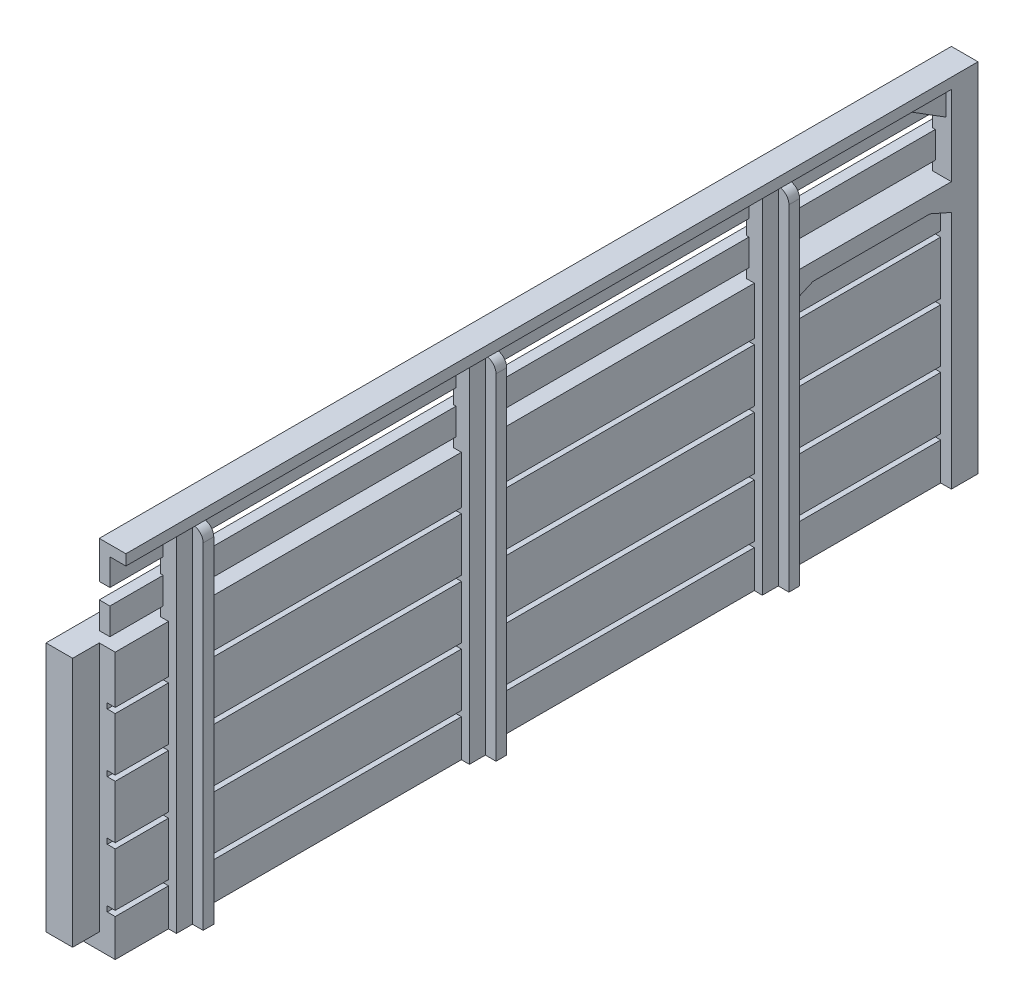
SolidWorks part; units mm, degrees
ref_plane "Front Plane" through (0, 0, 0) normal (0, 0, 1) x (1, 0, 0)
ref_plane "Top Plane" through (0, 0, 0) normal (0, 1, 0) x (1, 0, 0)
ref_plane "Right Plane" through (0, 0, 0) normal (1, 0, 0) x (0, 0, -1)
sketch "Sketch1" plane through (0, 0, 0) normal (1, 0, 0) x (0, 0, -1)
  line L1 (-80, 25) -> (80, 25)
  line L2 (-80, 25) -> (-80, -25)
  line L3 (-80, -25) -> (80, -25)
  line L4 (80, 25) -> (80, -25)
  line L5 (-80, 25) -> (80, -25) construction
  line L6 (-80, -25) -> (80, 25) construction
  point P0 (0, 0)
  dimension "D1" = 50
  dimension "D2" = 160
extrude "Boss-Extrude1" add sketch "Sketch1" along normal blind 3
sketch "Sketch2" plane through (3, 0, 0) normal (1, 0, 0) x (0, 0, -1)
  line L0 (-80, 25) -> (-80, -25) construction
  line L1 (-80, -17) -> (80, -17)
  line L2 (-80, -17) -> (-80, -18)
  line L3 (-80, -18) -> (80, -18)
  line L4 (80, -17) -> (80, -18)
  line L5 (80, -25) -> (80, 25) construction
  line L6 (-80, -25) -> (80, -25) construction
  line L8 (-80, -6) -> (80, -6)
  line L9 (-80, -6) -> (-80, -7)
  line L10 (-80, -7) -> (80, -7)
  line L11 (80, -6) -> (80, -7)
  line L12 (-80, 5) -> (80, 5)
  line L13 (-80, 5) -> (-80, 4)
  line L14 (-80, 4) -> (80, 4)
  line L15 (80, 5) -> (80, 4)
  line L16 (-80, 16) -> (80, 16)
  line L17 (-80, 16) -> (-80, 15)
  line L18 (-80, 15) -> (80, 15)
  line L19 (80, 16) -> (80, 15)
  dimension "D1" = 1
  dimension "D2" = 7
  dimension "D3" = 1
  dimension "D4" = 10
  dimension "D5" = 1
  dimension "D6" = 10
  dimension "D7" = 1
  dimension "D8" = 10
extrude "Cut-Extrude1" cut sketch "Sketch2" against normal blind 1.5
sketch "Sketch3" plane through (3, 0, 0) normal (1, 0, 0) x (0, 0, -1)
  line L0 (-80, -25) -> (80, -25) construction
  line L1 (80, -25) -> (75, -25)
  line L2 (80, -25) -> (80, 40)
  line L3 (80, 40) -> (75, 40)
  line L4 (75, -25) -> (75, 40)
  line L5 (45, -25) -> (40, -25)
  line L6 (45, -25) -> (45, 40)
  line L7 (45, 40) -> (40, 40)
  line L8 (40, -25) -> (40, 40)
  line L10 (-10, -25) -> (-15, -25)
  line L11 (-10, -25) -> (-10, 40)
  line L12 (-10, 40) -> (-15, 40)
  line L13 (-15, -25) -> (-15, 40)
  line L14 (-65, -25) -> (-70, -25)
  line L15 (-65, -25) -> (-65, 40)
  line L16 (-65, 40) -> (-70, 40)
  line L17 (-70, -25) -> (-70, 40)
  dimension "D1" = 65
  dimension "D2" = 5
  dimension "D3" = 65
  dimension "D4" = 30
  dimension "D5" = 5
  dimension "D6" = 5
  dimension "D7" = 65
  dimension "D8" = 50
  dimension "D9" = 50
  dimension "D10" = 5
  dimension "D11" = 65
extrude "Boss-Extrude2" add sketch "Sketch3" along normal mid plane 3
sketch "Sketch4" plane through (4.5, 0, 0) normal (1, 0, 0) x (0, 0, -1)
  line L0 (40, -25) -> (45, -25) construction
  line L1 (45, 40) -> (43, 40)
  line L2 (45, 40) -> (45, -25)
  line L3 (45, -25) -> (43, -25)
  line L4 (43, 40) -> (43, -25)
  line L5 (-10, 40) -> (-15, 40) construction
  line L6 (-10, -25) -> (-12, -25)
  line L7 (-10, -25) -> (-10, 40)
  line L8 (-10, 40) -> (-12, 40)
  line L9 (-12, -25) -> (-12, 40)
  line L10 (-65, 40) -> (-70, 40) construction
  line L11 (-65, -25) -> (-67, -25)
  line L12 (-65, -25) -> (-65, 40)
  line L13 (-65, 40) -> (-67, 40)
  line L14 (-67, -25) -> (-67, 40)
  dimension "D1" = 2
  dimension "D3" = 2
  dimension "D4" = 2
extrude "Boss-Extrude3" add sketch "Sketch4" along normal blind 2
fillet "Fillet1" radius 2 3 edges at (6.5, 40, -44) (6.5, 40, 11) (6.5, 40, 66)
sketch "Sketch5" plane through (0, 0, 0) normal (-1, 0, 0) x (0, 0, 1)
  line L7 (-80, 25) -> (-80, 40) construction
  line L12 (-80, 27) -> (80, 27)
  line L13 (-80, 27) -> (-80, 32)
  line L14 (-80, 32) -> (80, 32)
  line L15 (80, 27) -> (80, 32)
  line L16 (-80, 25) -> (80, 25) construction
  line L17 (-80, 35) -> (80, 35)
  line L18 (-80, 35) -> (-80, 40)
  line L19 (-80, 40) -> (80, 40)
  line L20 (80, 35) -> (80, 40)
  dimension "D1" = 5
  dimension "D2" = 5
  dimension "D3" = 160
  dimension "D4" = 160
  dimension "D5" = 2
  dimension "D6" = 3
extrude "Boss-Extrude4" add sketch "Sketch5" against normal blind 2
sketch "Sketch6" plane through (0, 40, 0) normal (0, 1, 0) x (1, 0, 0)
  line L8 (0, 80) -> (5, 80)
  line L9 (0, 80) -> (0, -80)
  line L10 (0, -80) -> (5, -80)
  line L11 (5, 80) -> (5, -80)
  dimension "D1" = 5
  dimension "D2" = 160
extrude "Boss-Extrude5" add sketch "Sketch6" along normal blind 2
sketch "Sketch9" plane through (4.5, 0, 0) normal (1, 0, 0) x (0, 0, -1)
  line L4 (80, -25) -> (80, 40)
  line L5 (80, 40) -> (75, 40)
  line L6 (75, 40) -> (75, -25)
  line L7 (75, -25) -> (80, -25)
  line L8 (80, -25) -> (80, 40)
  line L9 (80, 40) -> (75, 40)
  line L10 (75, 40) -> (75, -25)
  line L11 (75, -25) -> (80, -25)
  dimension "D1" = 0
extrude "Boss-Extrude8" add sketch "Sketch9" along normal up to surface (0.5 mm away) up to face at (5, 41, 0)
sketch "Sketch10" plane through (0, 0, 0) normal (-1, 0, 0) x (0, 0, 1)
  line L0 (80, 25) -> (80, -25) construction
  line L1 (-80, -25) -> (80, -25)
  line L2 (-80, -25) -> (-80, -22)
  line L3 (-80, -22) -> (80, -22)
  line L4 (80, -25) -> (80, -22)
  dimension "D1" = 3
extrude "Boss-Extrude9" add sketch "Sketch10" along normal blind 5
sketch "Sketch11" plane through (0, -22, 0) normal (0, 1, 0) x (1, 0, 0)
  line L0 (0, -80) -> (0, 80) construction
  line L1 (-5, 80) -> (0, 80)
  line L2 (-5, 80) -> (-5, 77)
  line L3 (-5, 77) -> (0, 77)
  line L4 (0, 80) -> (0, 77)
  dimension "D1" = 3
extrude "Boss-Extrude10" add sketch "Sketch11" along normal up to surface (47 mm away) up to face at (2, 25, 0)
sketch "Sketch12" plane through (3, 0, 0) normal (1, 0, 0) x (0, 0, -1)
  line L0 (-70, -18) -> (-70, -25) construction
sketch "Sketch13" plane through (0, 0, 0) normal (-1, 0, 0) x (0, 0, 1)
  line L0 (80, -22) -> (-77, -22) construction
  line L1 (75, -22) -> (85, -22)
  line L2 (75, -22) -> (75, 24.7147)
  line L3 (75, 24.7147) -> (85, 24.7147)
  line L4 (85, -22) -> (85, 24.7147)
  line L5 (80, 25) -> (80, -22) construction
  dimension "D1" = 10
  dimension "D2" = 5
extrude "Boss-Extrude11" add sketch "Sketch13" along normal up to surface (5 mm away) up to face at (-5, -7.3333, -25.6667)
sketch "Sketch14" plane through (2, 0, 0) normal (1, 0, 0) x (0, 0, -1)
  line L0 (75, 40) -> (75, 35) construction
  line L1 (75, 40) -> (75, 35)
  line L2 (45, 40) -> (75, 40) construction
  line L3 (67, 40) -> (75, 40)
  line L4 (75, 35) -> (67, 40)
  dimension "D1" = 8
extrude "Boss-Extrude12" add sketch "Sketch14" along normal blind 2
sketch "Sketch15" plane through (3, 0, 0) normal (1, 0, 0) x (0, 0, -1)
  line L0 (75, 25) -> (45, 25) construction
  line L1 (75, 25) -> (45, 25)
  line L2 (45, 25) -> (45, 20)
  line L3 (45, 25) -> (45, 16) construction
  line L4 (45, 20) -> (49, 21.7743)
  line L5 (49, 21.7743) -> (71, 21.7743)
  line L6 (71, 21.7743) -> (75, 20)
  line L7 (75, 20) -> (75, 25)
  dimension "D1" = 5
  dimension "D2" = 5
  dimension "D3" = 4
  dimension "D4" = 4
extrude "Boss-Extrude13" add sketch "Sketch15" along normal blind 2
sketch "Sketch16" plane through (0, 24.7147, 0) normal (0, 1, 0) x (1, 0, 0)
  line L5 (0, -75) -> (-5, -75)
  line L6 (-5, -75) -> (-5, -85)
  line L7 (-5, -85) -> (0, -85)
  line L8 (0, -85) -> (0, -80)
  line L9 (0, -80) -> (0, -75)
  line L10 (0, -75) -> (-5, -75)
  line L11 (-5, -75) -> (-5, -85)
  line L12 (-5, -85) -> (0, -85)
  line L13 (0, -85) -> (0, -80)
  line L14 (0, -80) -> (0, -75)
  dimension "D1" = 0
extrude "Boss-Extrude14" add sketch "Sketch16" along normal up to surface (0.2853 mm away) up to face at (1.5, 25, -7.7)
